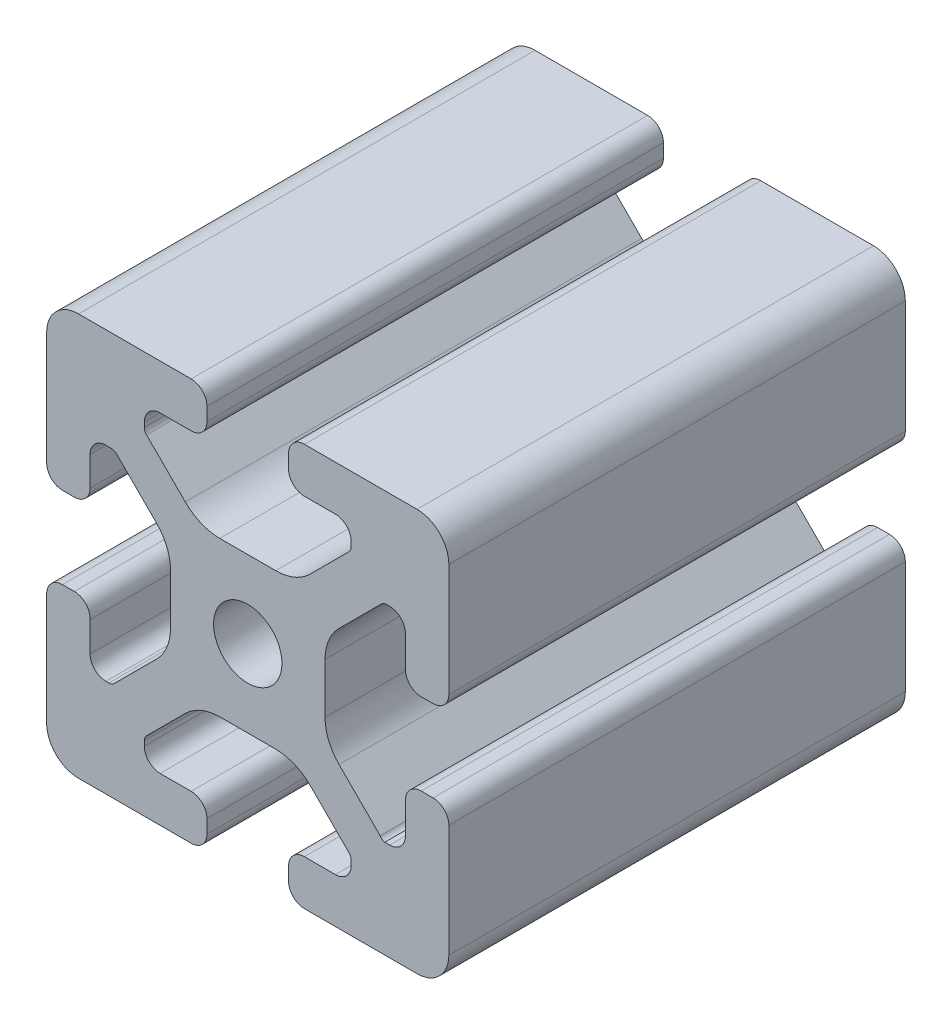
SolidWorks part; units mm, degrees
material "6105-T5 Aluminum"
ref_plane "Front Plane" through (0, 0, 0) normal (0, 0, 1) x (1, 0, 0)
ref_plane "Top Plane" through (0, 0, 0) normal (0, 1, 0) x (1, 0, 0)
ref_plane "Right Plane" through (0, 0, 0) normal (1, 0, 0) x (0, 0, -1)
sketch "Sketch1" plane through (0, 0, 0) normal (0, 0, 1) x (1, 0, 0)
  line L0 (0, 19.7407) -> (0, -19.7407) construction
  line L1 (19.0335, 0) -> (-20.7246, 0) construction
  line L2 (-8.715, -15.5246) -> (-5.63, -15.5246)
  line L3 (-10.285, -13.9546) -> (-10.285, -13.4925)
  line L4 (-6.2171, -9.1098) -> (-10.0624, -12.9551)
  line L5 (2.7773, -7.685) -> (-2.7773, -7.685)
  line L6 (10.0624, -12.9551) -> (6.2171, -9.1098)
  line L7 (10.285, -13.9546) -> (10.285, -13.4925)
  line L8 (5.63, -15.5246) -> (8.715, -15.5246)
  line L9 (4.06, -18.43) -> (4.06, -17.0946)
  line L10 (-4.06, -18.43) -> (-4.06, -17.0946)
  line L11 (15.68, -8.7154) -> (15.68, -5.63)
  line L12 (-14.11, -10.2854) -> (-13.8169, -10.2854)
  line L13 (20, -16.83) -> (20, -5.63)
  line L14 (20, 5.63) -> (20, 13.0011)
  line L15 (-16.83, 20) -> (-5.63, 20)
  line L16 (5.63, 20) -> (12.9796, 20)
  line L18 (-8.715, 15.5246) -> (-5.63, 15.5246)
  line L19 (-20, -17.0184) -> (-20, -5.7579)
  line L20 (-20, 5.573) -> (-20, 13.0045)
  line L21 (-15.68, -8.7154) -> (-15.68, -5.7579)
  line L23 (-16.6746, -20) -> (-5.63, -20)
  line L24 (5.63, -20) -> (13, -20)
  line L53 (14.11, -10.2854) -> (13.6201, -10.2854)
  line L54 (13.1637, -9.947) -> (9.0762, -5.8595)
  line L55 (7.685, -2.5008) -> (7.685, 2.5008)
  line L56 (9.0762, 5.8595) -> (13.2795, 10.0628)
  line L57 (13.8169, 10.2854) -> (14.11, 10.2854)
  line L58 (15.68, 8.7154) -> (15.68, 5.63)
  line L59 (17.25, 4.06) -> (18.43, 4.06)
  line L61 (20, 13.0011) -> (20, 16.83)
  line L62 (16.83, 20) -> (12.9796, 20)
  line L64 (4.06, 18.43) -> (4.06, 17.0946)
  line L65 (5.63, 15.5246) -> (8.715, 15.5246)
  line L66 (10.285, 13.9546) -> (10.285, 13.4925)
  line L67 (10.0624, 12.9551) -> (6.2171, 9.1098)
  line L68 (2.7773, 7.685) -> (-2.7773, 7.685)
  line L69 (-6.2171, 9.1098) -> (-10.0624, 12.9551)
  line L70 (-10.285, 13.4925) -> (-10.285, 13.9546)
  line L72 (-4.06, 17.0946) -> (-4.06, 18.43)
  line L75 (-20, 16.83) -> (-20, 13.0045)
  line L77 (-18.43, 4.003) -> (-17.25, 4.003)
  line L78 (-15.68, 5.573) -> (-15.68, 8.4757)
  line L79 (-14.0552, 10.0447) -> (-13.7199, 10.033)
  line L80 (-13.0405, 9.8238) -> (-9.0762, 5.8595)
  line L81 (-7.685, 2.5008) -> (-7.685, -2.5008)
  line L82 (-9.0762, -5.8595) -> (-13.2795, -10.0628)
  line L85 (-17.25, -4.1204) -> (-18.43, -4.1204)
  line L100 (13, -20) -> (16.83, -20)
  line L103 (18.43, -4.06) -> (17.25, -4.06)
  arc A0 (-5.63, -15.5246) -> (-4.06, -17.0946) centre (-5.63, -17.0946) cw
  arc A1 (-8.715, -15.5246) -> (-10.285, -13.9546) centre (-8.715, -13.9546) cw
  arc A2 (-10.285, -13.4925) -> (-10.0624, -12.9551) centre (-9.525, -13.4925) cw
  arc A3 (-6.2171, -9.1098) -> (-2.7773, -7.685) centre (-2.7773, -12.5496) cw
  arc A4 (2.7773, -7.685) -> (6.2171, -9.1098) centre (2.7773, -12.5496) cw
  arc A5 (10.0624, -12.9551) -> (10.285, -13.4925) centre (9.525, -13.4925) cw
  arc A6 (10.285, -13.9546) -> (8.715, -15.5246) centre (8.715, -13.9546) cw
  arc A7 (4.06, -17.0946) -> (5.63, -15.5246) centre (5.63, -17.0946) cw
  arc A8 (5.63, -20) -> (4.06, -18.43) centre (5.63, -18.43) cw
  arc A9 (-4.06, -18.43) -> (-5.63, -20) centre (-5.63, -18.43) cw
  circle A45 centre (0, 0) radius 3.4
  arc A46 (17.25, -4.06) -> (15.68, -5.63) centre (17.25, -5.63) ccw
  arc A47 (14.11, -10.2854) -> (15.68, -8.7154) centre (14.11, -8.7154) ccw
  arc A48 (13.1637, -9.947) -> (13.6201, -10.2854) centre (13.8117, -9.55) ccw
  arc A49 (7.685, -2.5008) -> (9.0762, -5.8595) centre (12.435, -2.5008) ccw
  arc A50 (9.0762, 5.8595) -> (7.685, 2.5008) centre (12.435, 2.5008) ccw
  arc A51 (13.8169, 10.2854) -> (13.2795, 10.0628) centre (13.8169, 9.5254) ccw
  arc A52 (15.68, 8.7154) -> (14.11, 10.2854) centre (14.11, 8.7154) ccw
  arc A53 (15.68, 5.63) -> (17.25, 4.06) centre (17.25, 5.63) ccw
  arc A54 (18.43, 4.06) -> (20, 5.63) centre (18.43, 5.63) ccw
  arc A55 (20, 16.83) -> (16.83, 20) centre (16.83, 16.83) ccw
  arc A56 (5.63, 20) -> (4.06, 18.43) centre (5.63, 18.43) ccw
  arc A57 (4.06, 17.0946) -> (5.63, 15.5246) centre (5.63, 17.0946) ccw
  arc A58 (10.285, 13.9546) -> (8.715, 15.5246) centre (8.715, 13.9546) ccw
  arc A59 (10.0624, 12.9551) -> (10.285, 13.4925) centre (9.525, 13.4925) ccw
  arc A60 (2.7773, 7.685) -> (6.2171, 9.1098) centre (2.7773, 12.5496) ccw
  arc A61 (-6.2171, 9.1098) -> (-2.7773, 7.685) centre (-2.7773, 12.5496) ccw
  arc A62 (-10.285, 13.4925) -> (-10.0624, 12.9551) centre (-9.525, 13.4925) ccw
  arc A63 (-8.715, 15.5246) -> (-10.285, 13.9546) centre (-8.715, 13.9546) ccw
  arc A64 (-5.63, 15.5246) -> (-4.06, 17.0946) centre (-5.63, 17.0946) ccw
  arc A65 (-4.06, 18.43) -> (-5.63, 20) centre (-5.63, 18.43) ccw
  arc A66 (-16.83, 20) -> (-20, 16.83) centre (-16.83, 16.83) ccw
  arc A67 (-20, 5.573) -> (-18.43, 4.003) centre (-18.43, 5.573) ccw
  arc A68 (-17.25, 4.003) -> (-15.68, 5.573) centre (-17.25, 5.573) ccw
  arc A69 (-14.0552, 10.0447) -> (-15.68, 8.4757) centre (-14.11, 8.4757) ccw
  arc A70 (-13.0405, 9.8238) -> (-13.7199, 10.033) centre (-13.5779, 9.2864) ccw
  arc A71 (-7.685, 2.5008) -> (-9.0762, 5.8595) centre (-12.435, 2.5008) ccw
  arc A72 (-9.0762, -5.8595) -> (-7.685, -2.5008) centre (-12.435, -2.5008) ccw
  arc A73 (-13.8169, -10.2854) -> (-13.2795, -10.0628) centre (-13.8169, -9.5254) ccw
  arc A74 (-15.68, -8.7154) -> (-14.11, -10.2854) centre (-14.11, -8.7154) ccw
  arc A75 (-15.68, -5.7579) -> (-17.25, -4.1204) centre (-17.2485, -5.6904) ccw
  arc A76 (-18.43, -4.1204) -> (-20, -5.7579) centre (-18.4315, -5.6904) ccw
  arc A77 (-20, -17.0184) -> (-16.6746, -20) centre (-16.8354, -16.8341) ccw
  arc A88 (16.83, -20) -> (20, -16.83) centre (16.83, -16.83) ccw
  arc A89 (20, -5.63) -> (18.43, -4.06) centre (18.43, -5.63) ccw
  dimension "D2" = 6.8
  dimension "D7" = 20.57
  dimension "D1" = 40
  dimension "D3" = 4.32
  dimension "D4" = 15.37
  dimension "D5" = 20
  dimension "D6" = 4.32
  dimension "D9" = 15.37
extrude "Extrude1" add sketch "Sketch1" against normal blind 45.4
